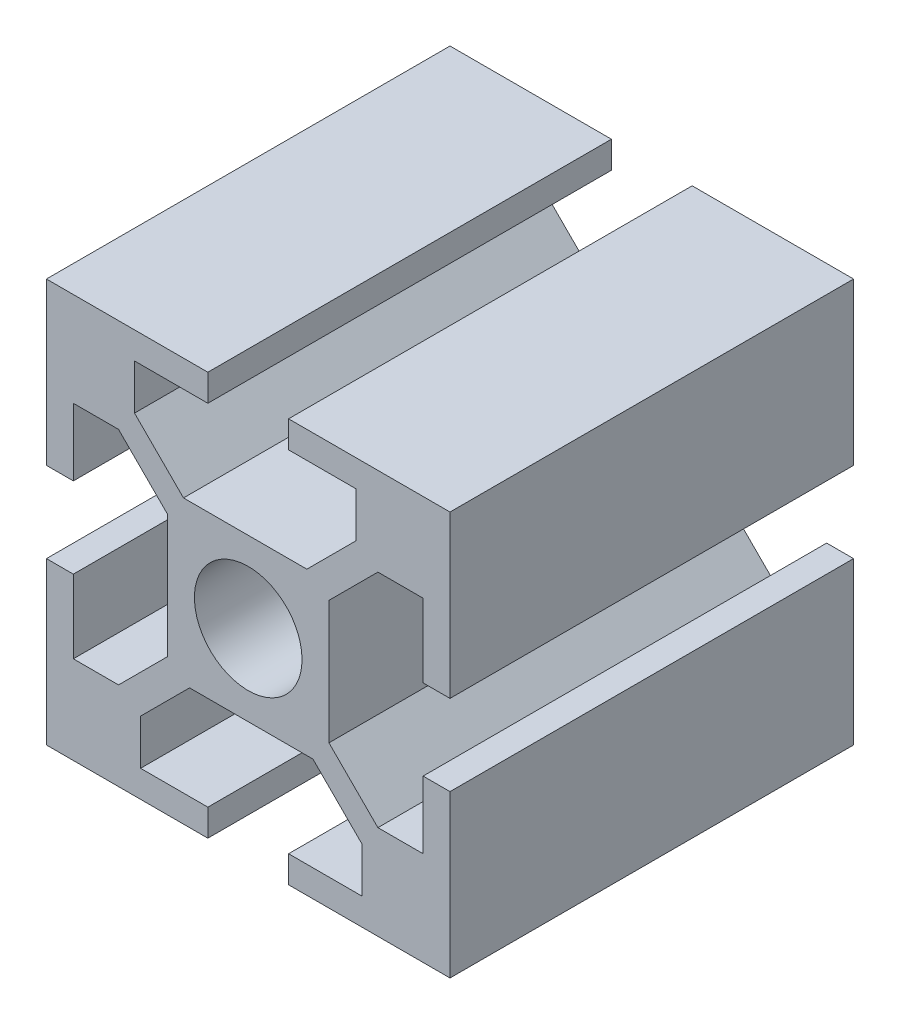
SolidWorks part; units mm, degrees
material "2014-O"
ref_plane "Front Plane" through (0, 0, 0) normal (0, 0, 1) x (1, 0, 0)
ref_plane "Top Plane" through (0, 0, 0) normal (0, 1, 0) x (1, 0, 0)
ref_plane "Right Plane" through (0, 0, 0) normal (1, 0, 0) x (0, 0, -1)
sketch "Sketch2" plane through (0, 0, 0) normal (0, 0, 1) x (1, 0, 0)
  line L1 (0, 6) -> (4.36, 6)
  line L2 (4.36, 6) -> (8, 9.64)
  line L3 (8, 9.64) -> (8, 13)
  line L4 (8, 13) -> (3, 13)
  line L5 (3, 13) -> (3, 15)
  line L6 (3, 15) -> (15, 15)
  line L7 (15, 15) -> (15, 3)
  line L8 (15, 3) -> (13, 3)
  line L9 (13, 3) -> (13, 8.4517)
  line L10 (13, 8.4517) -> (9.64, 8.4517)
  line L11 (9.64, 8.4517) -> (6, 4.8116)
  line L12 (6, 4.8116) -> (6, 0)
  line L15 (10, 10) -> (13, 10)
  line L16 (10, 10) -> (10, 13)
  line L17 (10, 13) -> (13, 13)
  line L18 (13, 10) -> (13, 13)
  line L19 (10, 10) -> (13, 13) construction
  line L20 (10, 13) -> (13, 10) construction
  line L21 (6, 0) -> (6, -4.36)
  line L22 (6, -4.36) -> (9.64, -8)
  line L23 (9.64, -8) -> (13, -8)
  line L24 (13, -8) -> (13, -3)
  line L25 (13, -3) -> (15, -3)
  line L26 (15, -3) -> (15, -15)
  line L27 (15, -15) -> (3, -15)
  line L28 (3, -15) -> (3, -13)
  line L29 (3, -13) -> (8.4517, -13)
  line L30 (8.4517, -13) -> (8.4517, -9.64)
  line L31 (8.4517, -9.64) -> (4.8116, -6)
  line L32 (4.8116, -6) -> (0, -6)
  line L34 (10, -10) -> (10, -13)
  line L35 (10, -10) -> (13, -10)
  line L36 (13, -10) -> (13, -13)
  line L37 (10, -13) -> (13, -13)
  line L38 (10, -10) -> (13, -13) construction
  line L39 (13, -10) -> (10, -13) construction
  line L41 (0, -6) -> (-4.36, -6)
  line L42 (-4.36, -6) -> (-8, -9.64)
  line L43 (-8, -9.64) -> (-8, -13)
  line L44 (-8, -13) -> (-3, -13)
  line L45 (-3, -13) -> (-3, -15)
  line L46 (-3, -15) -> (-15, -15)
  line L47 (-15, -15) -> (-15, -3)
  line L48 (-15, -3) -> (-13, -3)
  line L49 (-13, -3) -> (-13, -8.4517)
  line L50 (-13, -8.4517) -> (-9.64, -8.4517)
  line L51 (-9.64, -8.4517) -> (-6, -4.8116)
  line L52 (-6, -4.8116) -> (-6, 0)
  line L54 (-10, -10) -> (-13, -10)
  line L55 (-10, -10) -> (-10, -13)
  line L56 (-10, -13) -> (-13, -13)
  line L57 (-13, -10) -> (-13, -13)
  line L58 (-10, -10) -> (-13, -13) construction
  line L59 (-10, -13) -> (-13, -10) construction
  line L61 (-6, 0) -> (-6, 4.36)
  line L62 (-6, 4.36) -> (-9.64, 8)
  line L63 (-9.64, 8) -> (-13, 8)
  line L64 (-13, 8) -> (-13, 3)
  line L65 (-13, 3) -> (-15, 3)
  line L66 (-15, 3) -> (-15, 15)
  line L67 (-15, 15) -> (-3, 15)
  line L68 (-3, 15) -> (-3, 13)
  line L69 (-3, 13) -> (-8.4517, 13)
  line L70 (-8.4517, 13) -> (-8.4517, 9.64)
  line L71 (-8.4517, 9.64) -> (-4.8116, 6)
  line L72 (-4.8116, 6) -> (0, 6)
  line L74 (-10, 10) -> (-10, 13)
  line L75 (-10, 10) -> (-13, 10)
  line L76 (-13, 10) -> (-13, 13)
  line L77 (-10, 13) -> (-13, 13)
  line L78 (-10, 10) -> (-13, 13) construction
  line L79 (-13, 10) -> (-10, 13) construction
  circle A0 centre (0, 0) radius 4
  point P0 (0, 0)
  point P8 (11.5, 11.5)
  point P29 (11.5, -11.5)
  point P47 (-11.5, -11.5)
  point P65 (-11.5, 11.5)
  point P77 (0, 0)
  dimension "D2" = 8
  dimension "D3" = 135
  dimension "D4" = 12
  dimension "D5" = 12
  dimension "D6" = 2
  dimension "D7" = 2
  dimension "D8" = 3
  dimension "D9" = 3
  dimension "D10" = 2
  dimension "D11" = 2
  dimension "D12" = 2
  dimension "D13" = 1.5483
  dimension "D14" = 2
  dimension "D15" = 15
  dimension "D16" = 15
  dimension "D17" = 4
extrude "Boss-Extrude2" add sketch "Sketch2" along normal blind 30
